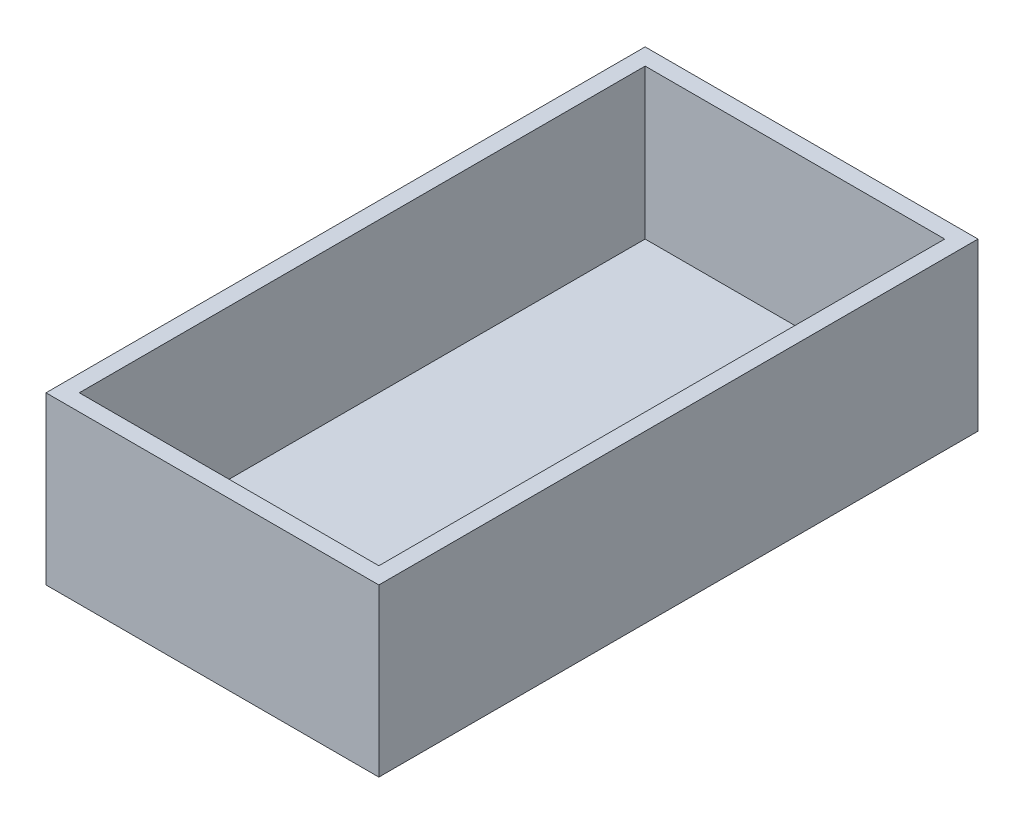
SolidWorks part; units mm, degrees
ref_plane "Front Plane" through (0, 0, 0) normal (0, 0, 1) x (1, 0, 0)
ref_plane "Top Plane" through (0, 0, 0) normal (0, 1, 0) x (1, 0, 0)
ref_plane "Right Plane" through (0, 0, 0) normal (1, 0, 0) x (0, 0, -1)
sketch "Sketch1" plane through (0, 0, 0) normal (0, 1, 0) x (1, 0, 0)
  line L1 (-20, 36) -> (20, 36)
  line L2 (-20, 36) -> (-20, -36)
  line L3 (-20, -36) -> (20, -36)
  line L4 (20, 36) -> (20, -36)
  line L5 (-20, 36) -> (20, -36) construction
  line L6 (-20, -36) -> (20, 36) construction
  point P0 (0, 0)
  dimension "D1" = 72
  dimension "D2" = 40
extrude "Boss-Extrude1" add sketch "Sketch1" along normal blind 20
shell "Shell1" thickness 2
